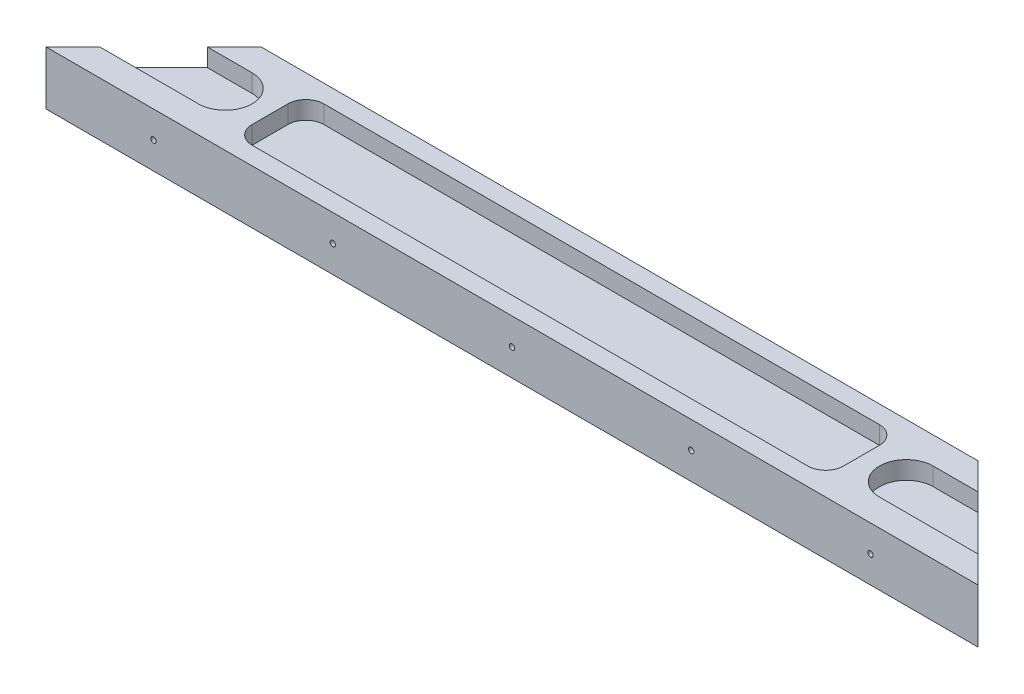
SolidWorks part; units mm, degrees
ref_plane "Front Plane" through (0, 0, 0) normal (0, 0, 1) x (1, 0, 0)
ref_plane "Top Plane" through (0, 0, 0) normal (0, 1, 0) x (1, 0, 0)
ref_plane "Right Plane" through (0, 0, 0) normal (1, 0, 0) x (0, 0, -1)
sketch "Sketch1" plane through (0, 0, 0) normal (0, 1, 0) x (1, 0, 0)
  line L0 (0, 0) -> (260, 0)
  line L1 (260, 0) -> (230, 30)
  line L2 (230, 30) -> (30, 30)
  line L3 (30, 30) -> (0, 0)
  point P3 (130, 30)
  point P6 (130, 0)
  dimension "D1" = 260
  dimension "D2" = 200
  dimension "D3" = 30
extrude "Boss-Extrude1" add sketch "Sketch1" along normal blind 15
sketch "Sketch2" plane through (0, 15, 0) normal (0, 1, 0) x (1, 0, 0)
  line L0 (-5, 15) -> (35, 15) construction
  line L1 (-5, 22.5) -> (35, 22.5)
  line L2 (-5, 7.5) -> (35, 7.5)
  line L3 (30, 30) -> (0, 0) construction
  line L4 (130, 30) -> (130, 0) construction
  line L5 (230, 30) -> (30, 30) construction
  line L6 (0, 0) -> (260, 0) construction
  line L7 (265, 15) -> (225, 15) construction
  line L8 (265, 22.5) -> (225, 22.5)
  line L9 (265, 7.5) -> (225, 7.5)
  arc A0 (-5, 22.5) -> (-5, 7.5) centre (-5, 15) ccw
  arc A1 (35, 7.5) -> (35, 22.5) centre (35, 15) ccw
  arc A2 (265, 22.5) -> (265, 7.5) centre (265, 15) cw
  arc A3 (225, 7.5) -> (225, 22.5) centre (225, 15) cw
  point P2 (15, 15)
  point P17 (245, 15)
  dimension "D1" = 40
  dimension "D2" = 15
extrude "Cut-Extrude1" cut sketch "Sketch2" against normal blind 5
sketch "Sketch3" plane through (0, 0, 0) normal (0, 0, 1) x (1, 0, 0)
  line L0 (0, 7.5) -> (260, 7.5) construction
  line L1 (0, 15) -> (0, 0) construction
  line L2 (260, 15) -> (260, 0) construction
  circle A0 centre (130, 7.5) radius 0.75
  circle A1 centre (180, 7.5) radius 0.75
  circle A2 centre (230, 7.5) radius 0.75
  circle A3 centre (80, 7.5) radius 0.75
  circle A4 centre (30, 7.5) radius 0.75
  dimension "D1" = 1.5
  dimension "D2" = 3
  dimension "D3" = 3
extrude "Cut-Extrude2" cut sketch "Sketch3" against normal up to surface (30 mm away) up to face at (130, 7.5, -30)
sketch "Sketch4" plane through (0, 15, 0) normal (0, 1, 0) x (1, 0, 0)
  line L0 (0, 0) -> (260, 0) construction
  line L1 (52.5, 25) -> (207.5, 25)
  line L2 (47.5, 20) -> (47.5, 10)
  line L3 (52.5, 5) -> (207.5, 5)
  line L4 (212.5, 20) -> (212.5, 10)
  line L5 (230, 30) -> (30, 30) construction
  arc A0 (35, 7.5) -> (35, 22.5) centre (35, 15) ccw construction
  arc A1 (225, 22.5) -> (225, 7.5) centre (225, 15) ccw construction
  arc A2 (52.5, 25) -> (47.5, 20) centre (52.5, 20) ccw
  arc A3 (47.5, 10) -> (52.5, 5) centre (52.5, 10) ccw
  arc A4 (207.5, 5) -> (212.5, 10) centre (207.5, 10) ccw
  arc A5 (207.5, 25) -> (212.5, 20) centre (207.5, 20) cw
  point P4 (42.5, 15)
  point P5 (217.5, 15)
  dimension "D5" = 5
  dimension "D1" = 5
  dimension "D2" = 5
  dimension "D3" = 5
  dimension "D4" = 5
extrude "Cut-Extrude3" cut sketch "Sketch4" against normal blind 5
